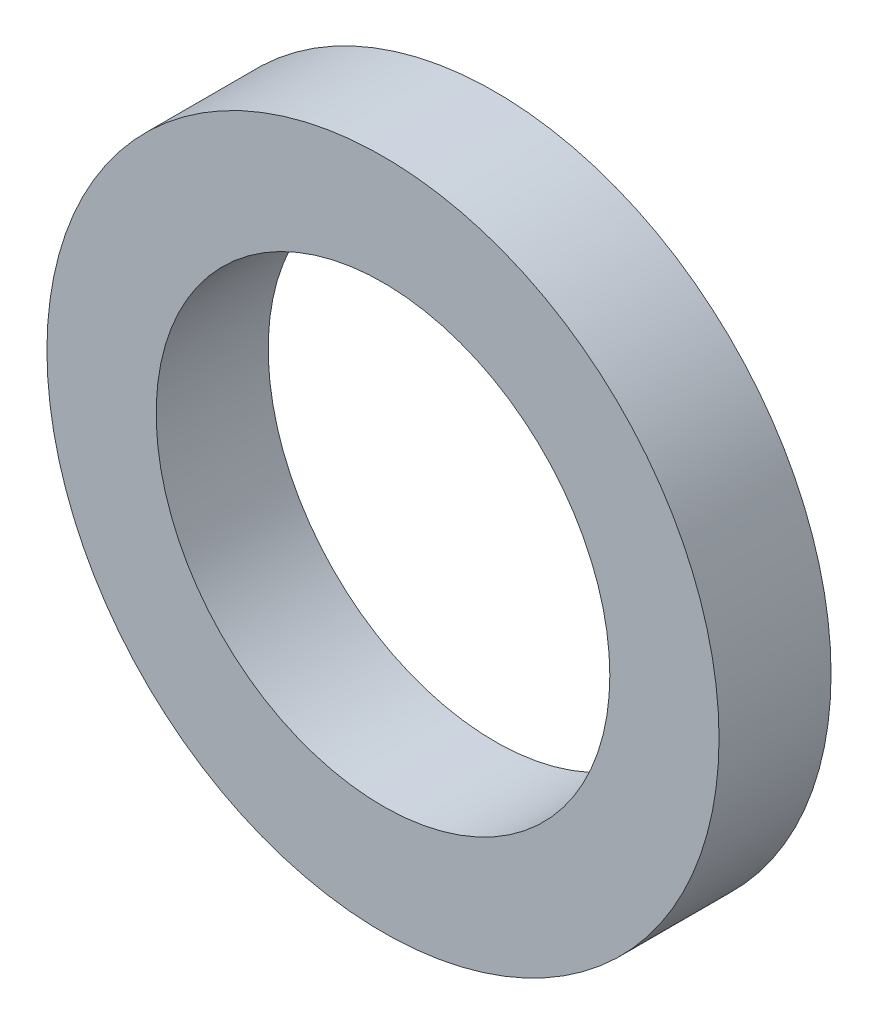
SolidWorks part; units mm, degrees
ref_plane "Front Plane" through (0, 0, 0) normal (0, 0, 1) x (1, 0, 0)
ref_plane "Top Plane" through (0, 0, 0) normal (0, 1, 0) x (1, 0, 0)
ref_plane "Right Plane" through (0, 0, 0) normal (1, 0, 0) x (0, 0, -1)
sketch "Sketch1" plane through (0, 0, 0) normal (0, 0, 1) x (1, 0, 0)
  circle A0 centre (0, 0) radius 2.025
  circle A1 centre (0, 0) radius 3
  dimension "D1" = 4.05
  dimension "D2" = 6
extrude "Boss-Extrude1" add sketch "Sketch1" along normal blind 1
